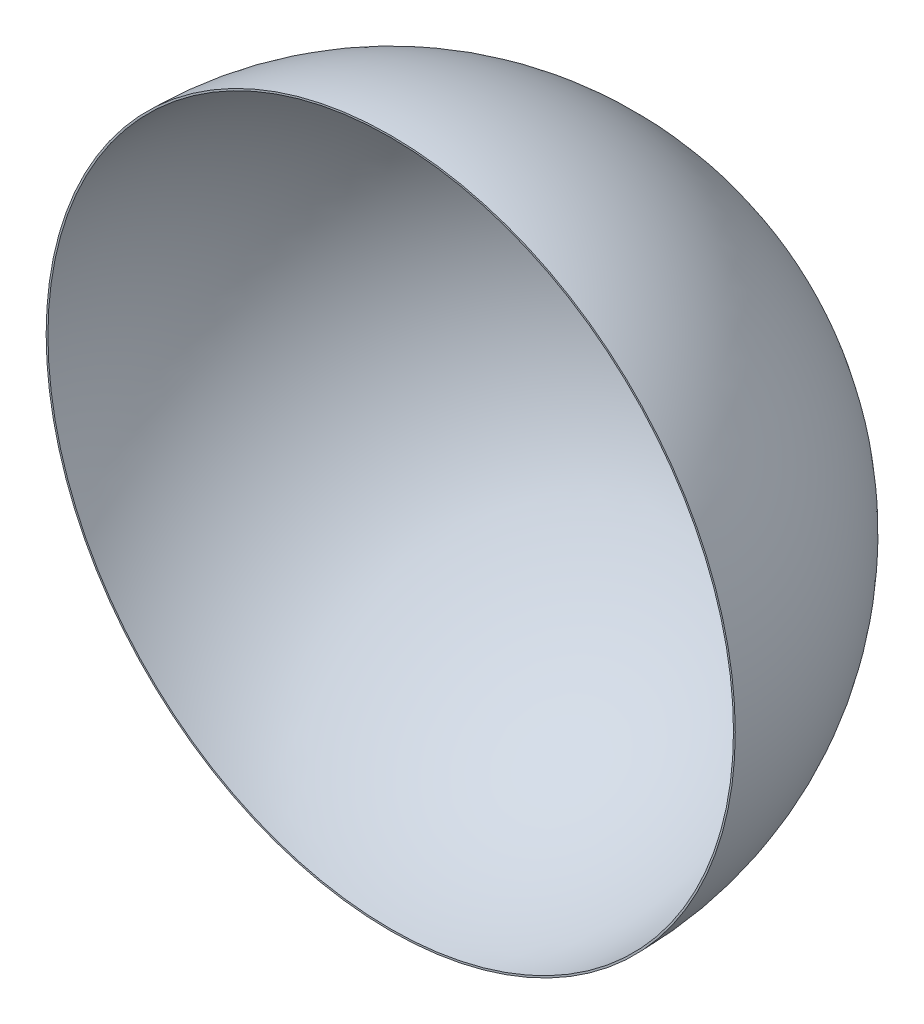
SolidWorks part; units mm, degrees
ref_plane "Front Plane" through (0, 0, 0) normal (0, 0, 1) x (1, 0, 0)
ref_plane "Top Plane" through (0, 0, 0) normal (0, 1, 0) x (1, 0, 0)
ref_plane "Right Plane" through (0, 0, 0) normal (1, 0, 0) x (0, 0, -1)
sketch "Sketch1" plane through (0, 0, 0) normal (0, 1, 0) x (1, 0, 0)
  line L0 (0, 0) -> (0, -4876.8) construction
  line L1 (0, -4876.8) -> (4876.8, -4876.8) construction
  line L2 (0, 0) -> (0, 25.4)
  line L3 (4876.8, -4876.8) -> (4902.2, -4876.8)
  arc A0 (0, 0) -> (4876.8, -4876.8) centre (0, -4876.8) cw
  arc A1 (0, 25.4) -> (4902.2, -4876.8) centre (0, -4876.8) cw
  point P5 (5108.0004, -4869.2802)
revolve "Revolve2" add sketch "Sketch1" angle 360 about L0
